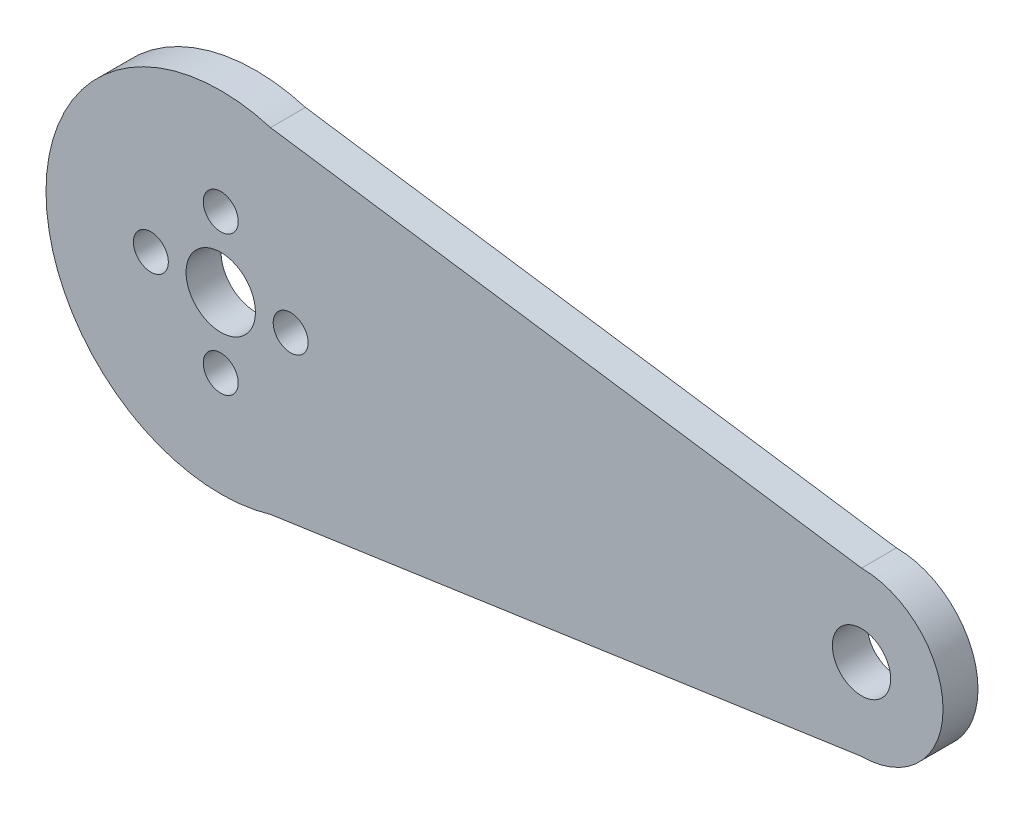
SolidWorks part; units mm, degrees
ref_plane "前视基准面" through (0, 0, 0) normal (0, 0, 1) x (1, 0, 0)
ref_plane "上视基准面" through (0, 0, 0) normal (0, 1, 0) x (1, 0, 0)
ref_plane "右视基准面" through (0, 0, 0) normal (1, 0, 0) x (0, 0, -1)
sketch "Sketch1" plane through (0, 0, 0) normal (0, 0, 1) x (1, 0, 0)
  circle A0 centre (-0.7599, 7.2505) radius 6 construction
  circle A1 centre (-0.7599, 7.2505) radius 2.9769
  circle A2 centre (-0.7599, 13.2505) radius 1.5
  circle A3 centre (-6.7599, 7.2505) radius 1.5
  circle A4 centre (-0.7599, 1.2505) radius 1.5
  circle A5 centre (5.2401, 7.2505) radius 1.5
  circle A6 centre (-0.7599, 7.2505) radius 15
  dimension "D1" = 12
  dimension "D2" = 30
extrude "Boss-Extrude1" add sketch "Sketch1" along normal blind 3
sketch "Sketch2" plane through (0, 0, 3) normal (0, 0, 1) x (1, 0, 0)
  line L0 (-0.7599, 7.2505) -> (54.2401, 7.2505) construction
  line L1 (-0.7599, 22.2505) -> (54.2401, 14.2505)
  line L2 (-0.7599, -7.7495) -> (54.2401, 0.2505)
  circle A0 centre (54.2401, 7.2505) radius 2.5
  circle A1 centre (54.2401, 7.2505) radius 7 construction
  circle A2 centre (-0.7599, 7.2505) radius 15 construction
  arc A3 (54.2401, 0.2505) -> (54.2401, 14.2505) centre (54.2401, 7.2505) ccw
  arc A5 (-0.7599, -7.7495) -> (-0.7599, 22.2505) centre (-8.4189, 7.2505) ccw
  dimension "D2" = 7
  dimension "D3" = 5
  dimension "D1" = 55
extrude "Boss-Extrude2" add sketch "Sketch2" against normal up to surface (3 mm away) up to face at (14.2401, 7.2505, 0)
